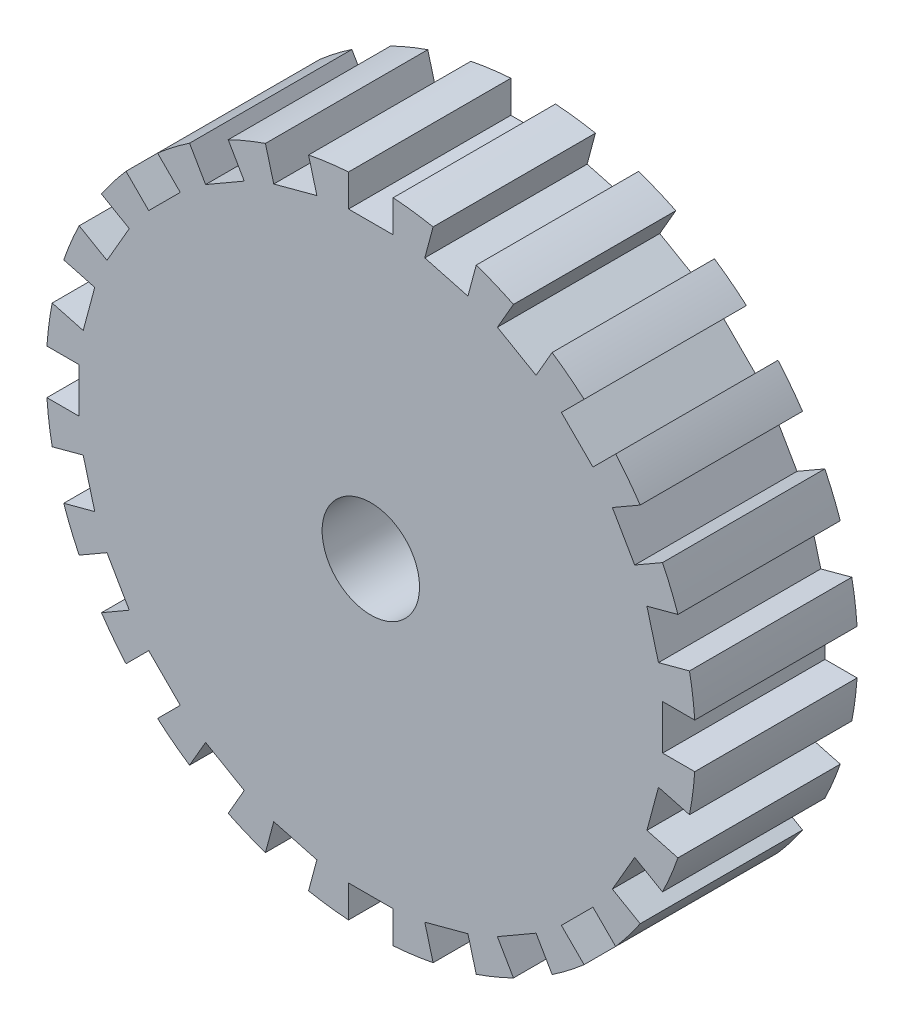
SolidWorks part; units mm, degrees
ref_plane "Front Plane" through (0, 0, 0) normal (0, 0, 1) x (1, 0, 0)
ref_plane "Top Plane" through (0, 0, 0) normal (0, 1, 0) x (1, 0, 0)
ref_plane "Right Plane" through (0, 0, 0) normal (1, 0, 0) x (0, 0, -1)
sketch "Sketch2" plane through (0, 0, 0) normal (0, 0, 1) x (1, 0, 0)
  circle A0 centre (0, 0) radius 40
  dimension "D1" = 80
extrude "Boss-Extrude1" add sketch "Sketch2" along normal blind 20
sketch "Sketch3" plane through (0, 0, 0) normal (0, 0, 1) x (1, 0, 0)
  line L0 (-6.6482, -35.4368) -> (-7.7638, -39.5999)
  line L1 (-2.75, -40.26) -> (2.75, -40.26)
  line L2 (-2.75, -40.26) -> (-2.75, -35.95)
  line L3 (-2.75, -35.95) -> (2.75, -35.95)
  line L4 (2.75, -35.95) -> (2.75, -40.26)
  line L5 (-11.9608, -34.0133) -> (-6.6482, -35.4368)
  line L6 (-13.0764, -38.1764) -> (-11.9608, -34.0133)
  line L7 (-13.0764, -38.1764) -> (-7.7638, -39.5999)
  line L8 (-15.5934, -32.5086) -> (-17.7484, -36.2412)
  line L9 (-20.3566, -29.7586) -> (-15.5934, -32.5086)
  line L10 (-22.5116, -33.4912) -> (-20.3566, -29.7586)
  line L11 (-22.5116, -33.4912) -> (-17.7484, -36.2412)
  line L12 (-23.4759, -27.365) -> (-26.5236, -30.4127)
  line L13 (-27.365, -23.4759) -> (-23.4759, -27.365)
  line L14 (-30.4127, -26.5236) -> (-27.365, -23.4759)
  line L15 (-30.4127, -26.5236) -> (-26.5236, -30.4127)
  line L16 (-29.7586, -20.3566) -> (-33.4912, -22.5116)
  line L17 (-32.5086, -15.5934) -> (-29.7586, -20.3566)
  line L18 (-36.2412, -17.7484) -> (-32.5086, -15.5934)
  line L19 (-36.2412, -17.7484) -> (-33.4912, -22.5116)
  line L20 (-34.0133, -11.9608) -> (-38.1764, -13.0764)
  line L21 (-35.4368, -6.6482) -> (-34.0133, -11.9608)
  line L22 (-39.5999, -7.7638) -> (-35.4368, -6.6482)
  line L23 (-39.5999, -7.7638) -> (-38.1764, -13.0764)
  line L24 (-35.95, -2.75) -> (-40.26, -2.75)
  line L25 (-35.95, 2.75) -> (-35.95, -2.75)
  line L26 (-40.26, 2.75) -> (-35.95, 2.75)
  line L27 (-40.26, 2.75) -> (-40.26, -2.75)
  line L28 (-35.4368, 6.6482) -> (-39.5999, 7.7638)
  line L29 (-34.0133, 11.9608) -> (-35.4368, 6.6482)
  line L30 (-38.1764, 13.0764) -> (-34.0133, 11.9608)
  line L31 (-38.1764, 13.0764) -> (-39.5999, 7.7638)
  line L32 (-32.5086, 15.5934) -> (-36.2412, 17.7484)
  line L33 (-29.7586, 20.3566) -> (-32.5086, 15.5934)
  line L34 (-33.4912, 22.5116) -> (-29.7586, 20.3566)
  line L35 (-33.4912, 22.5116) -> (-36.2412, 17.7484)
  line L36 (-27.365, 23.4759) -> (-30.4127, 26.5236)
  line L37 (-23.4759, 27.365) -> (-27.365, 23.4759)
  line L38 (-26.5236, 30.4127) -> (-23.4759, 27.365)
  line L39 (-26.5236, 30.4127) -> (-30.4127, 26.5236)
  line L40 (-20.3566, 29.7586) -> (-22.5116, 33.4912)
  line L41 (-15.5934, 32.5086) -> (-20.3566, 29.7586)
  line L42 (-17.7484, 36.2412) -> (-15.5934, 32.5086)
  line L43 (-17.7484, 36.2412) -> (-22.5116, 33.4912)
  line L44 (-11.9608, 34.0133) -> (-13.0764, 38.1764)
  line L45 (-6.6482, 35.4368) -> (-11.9608, 34.0133)
  line L46 (-7.7638, 39.5999) -> (-6.6482, 35.4368)
  line L47 (-7.7638, 39.5999) -> (-13.0764, 38.1764)
  line L48 (-2.75, 35.95) -> (-2.75, 40.26)
  line L49 (2.75, 35.95) -> (-2.75, 35.95)
  line L50 (2.75, 40.26) -> (2.75, 35.95)
  line L51 (2.75, 40.26) -> (-2.75, 40.26)
  line L52 (6.6482, 35.4368) -> (7.7638, 39.5999)
  line L53 (11.9608, 34.0133) -> (6.6482, 35.4368)
  line L54 (13.0764, 38.1764) -> (11.9608, 34.0133)
  line L55 (13.0764, 38.1764) -> (7.7638, 39.5999)
  line L56 (15.5934, 32.5086) -> (17.7484, 36.2412)
  line L57 (20.3566, 29.7586) -> (15.5934, 32.5086)
  line L58 (22.5116, 33.4912) -> (20.3566, 29.7586)
  line L59 (22.5116, 33.4912) -> (17.7484, 36.2412)
  line L60 (23.4759, 27.365) -> (26.5236, 30.4127)
  line L61 (27.365, 23.4759) -> (23.4759, 27.365)
  line L62 (30.4127, 26.5236) -> (27.365, 23.4759)
  line L63 (30.4127, 26.5236) -> (26.5236, 30.4127)
  line L64 (29.7586, 20.3566) -> (33.4912, 22.5116)
  line L65 (32.5086, 15.5934) -> (29.7586, 20.3566)
  line L66 (36.2412, 17.7484) -> (32.5086, 15.5934)
  line L67 (36.2412, 17.7484) -> (33.4912, 22.5116)
  line L68 (34.0133, 11.9608) -> (38.1764, 13.0764)
  line L69 (35.4368, 6.6482) -> (34.0133, 11.9608)
  line L70 (39.5999, 7.7638) -> (35.4368, 6.6482)
  line L71 (39.5999, 7.7638) -> (38.1764, 13.0764)
  line L72 (35.95, 2.75) -> (40.26, 2.75)
  line L73 (35.95, -2.75) -> (35.95, 2.75)
  line L74 (40.26, -2.75) -> (35.95, -2.75)
  line L75 (40.26, -2.75) -> (40.26, 2.75)
  line L76 (35.4368, -6.6482) -> (39.5999, -7.7638)
  line L77 (34.0133, -11.9608) -> (35.4368, -6.6482)
  line L78 (38.1764, -13.0764) -> (34.0133, -11.9608)
  line L79 (38.1764, -13.0764) -> (39.5999, -7.7638)
  line L80 (32.5086, -15.5934) -> (36.2412, -17.7484)
  line L81 (29.7586, -20.3566) -> (32.5086, -15.5934)
  line L82 (33.4912, -22.5116) -> (29.7586, -20.3566)
  line L83 (33.4912, -22.5116) -> (36.2412, -17.7484)
  line L84 (27.365, -23.4759) -> (30.4127, -26.5236)
  line L85 (23.4759, -27.365) -> (27.365, -23.4759)
  line L86 (26.5236, -30.4127) -> (23.4759, -27.365)
  line L87 (26.5236, -30.4127) -> (30.4127, -26.5236)
  line L88 (20.3566, -29.7586) -> (22.5116, -33.4912)
  line L89 (15.5934, -32.5086) -> (20.3566, -29.7586)
  line L90 (17.7484, -36.2412) -> (15.5934, -32.5086)
  line L91 (17.7484, -36.2412) -> (22.5116, -33.4912)
  line L92 (11.9608, -34.0133) -> (13.0764, -38.1764)
  line L93 (6.6482, -35.4368) -> (11.9608, -34.0133)
  line L94 (7.7638, -39.5999) -> (6.6482, -35.4368)
  line L95 (7.7638, -39.5999) -> (13.0764, -38.1764)
  point P6 (0, -40.26)
  dimension "D1" = 35.95
  dimension "D2" = 4.31
  dimension "D3" = 5.5
  dimension "D4" = 2.75
  dimension "D6" = 0.5132
  dimension "D7" = 3.8982
  dimension "D5" = 24
extrude "Cut-Extrude1" cut sketch "Sketch3" along normal up to surface (20 mm away) up to face at (40, 0, 20)
sketch "Sketch4" plane through (0, 0, 0) normal (0, 0, 1) x (1, 0, 0)
  circle A0 centre (0, 0) radius 6
  dimension "D1" = 12
extrude "Cut-Extrude2" cut sketch "Sketch4" along normal up to surface (20 mm away) up to face at (0, 0, 20)
